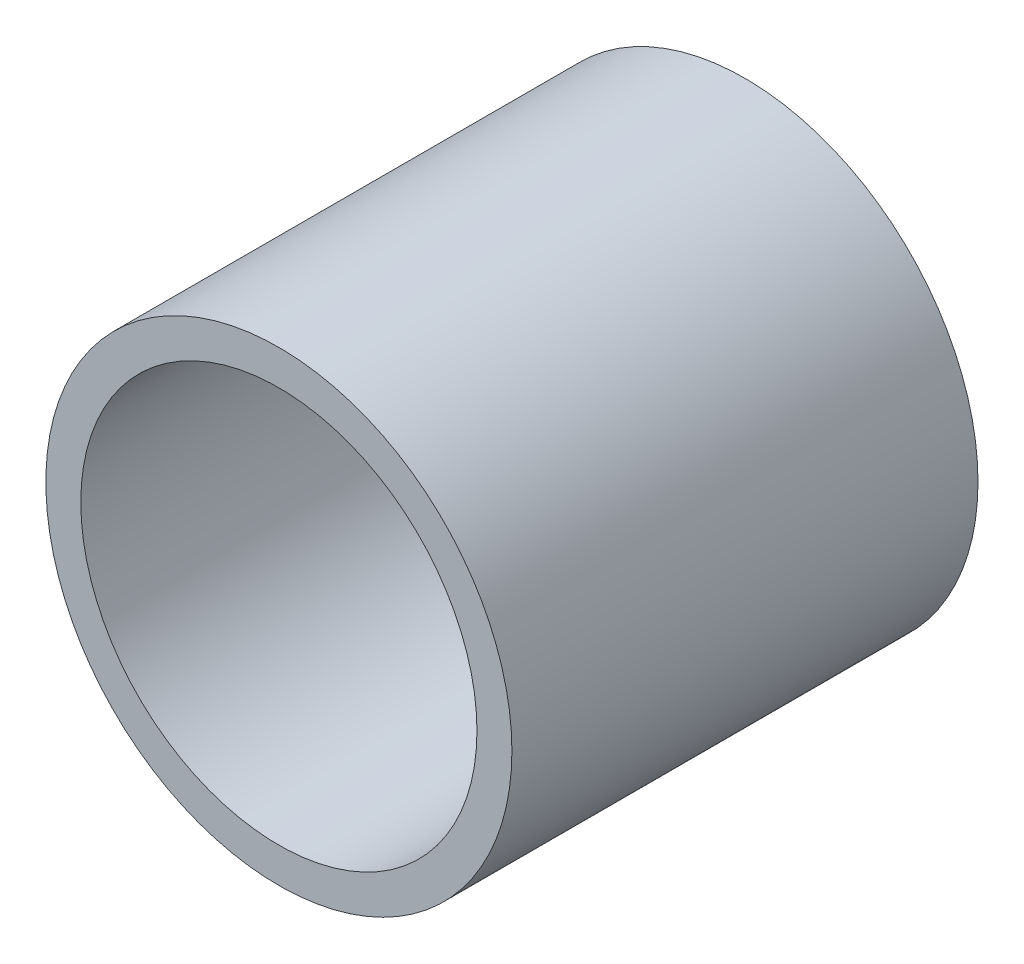
SolidWorks part; units mm, degrees
ref_plane "Plan de face" through (0, 0, 0) normal (0, 0, 1) x (1, 0, 0)
ref_plane "Plan de dessus" through (0, 0, 0) normal (0, 1, 0) x (1, 0, 0)
ref_plane "Plan de droite" through (0, 0, 0) normal (1, 0, 0) x (0, 0, -1)
sketch "Esquisse1" plane through (0, 0, 0) normal (0, 0, 1) x (1, 0, 0)
  circle A0 centre (0, 0) radius 40
  dimension "D1" = 80
extrude "Extru.-Mince1" add sketch "Esquisse1" along normal blind 80 thin thin type one direction reverse wall 6
